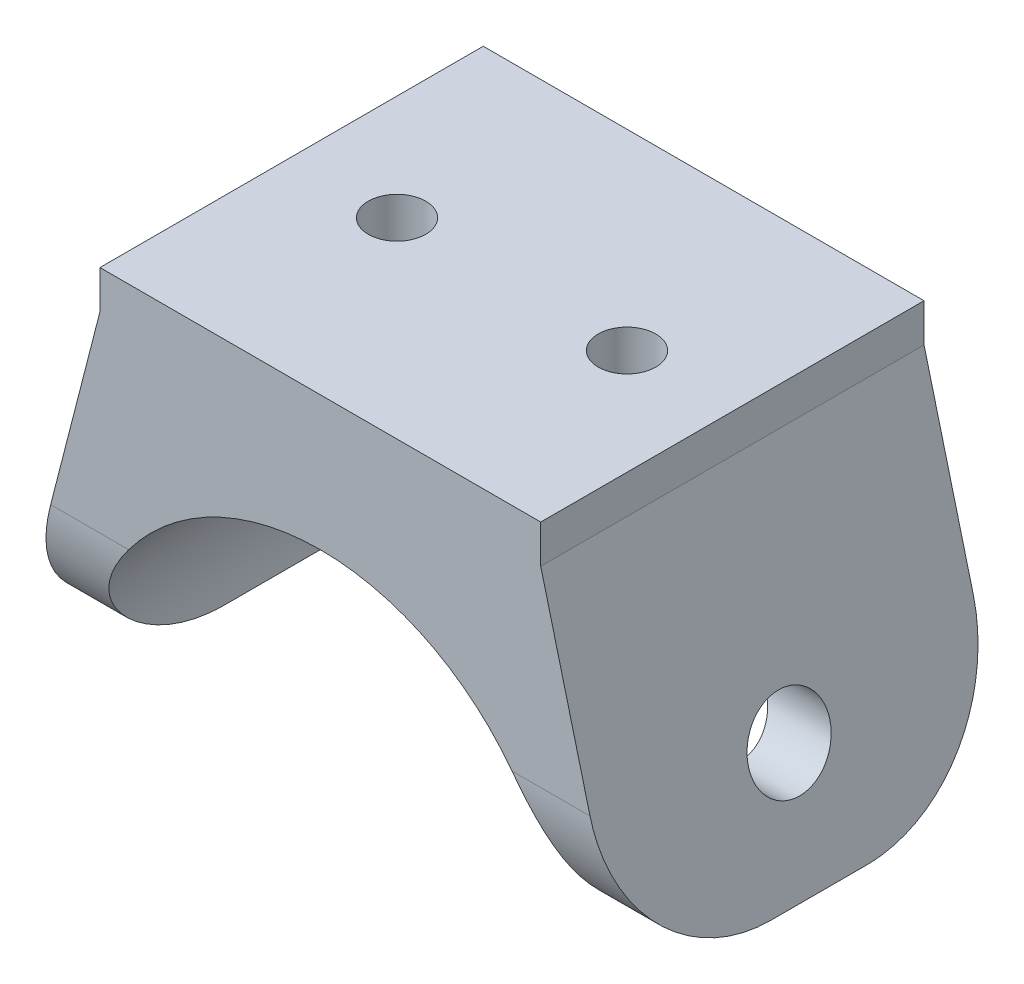
SolidWorks part; units mm, degrees
ref_plane "前基準面" through (0, 0, 0) normal (0, 0, 1) x (1, 0, 0)
ref_plane "上基準面" through (0, 0, 0) normal (0, 1, 0) x (1, 0, 0)
ref_plane "右基準面" through (0, 0, 0) normal (1, 0, 0) x (0, 0, -1)
sketch "草圖1" plane through (0, 0, 0) normal (0, 0, 1) x (1, 0, 0)
  line L0 (-23, 35) -> (-32, 0)
  line L1 (-23, 39) -> (23, 39)
  line L2 (-23, 39) -> (-23, 35)
  line L4 (23, 39) -> (23, 35)
  line L5 (-32, 0) -> (-25, 0)
  line L6 (32, 0) -> (23, 35)
  line L7 (25, 0) -> (32, 0)
  arc A0 (25, 0) -> (-25, 0) centre (0, 0) ccw
  dimension "D4" = 50
  dimension "D1" = 46
  dimension "D2" = 4
  dimension "D3" = 64
  dimension "D5" = 39
extrude "填料-伸長1" add sketch "草圖1" along normal blind 40
sketch "草圖2" plane through (0, 39, 0) normal (0, 1, 0) x (1, 0, 0)
  line L0 (0, 5.4826) -> (0, -42.1633) construction
  line L1 (-36.6182, -20) -> (35.4385, -20) construction
  circle A0 centre (-12, -20) radius 3
  circle A1 centre (12, -20) radius 3
  dimension "D1" = 6
  dimension "D2" = 6
  dimension "D3" = 12
  dimension "D4" = 12
extrude "除料-伸長1" cut sketch "草圖2" against normal blind 14
sketch "草圖3" plane through (0, 0, 0) normal (1, 0, 0) x (0, 0, -1)
  line L0 (-20, 44.9808) -> (-20, -1.3539) construction
  line L1 (-40, 39) -> (0, 39) construction
  circle A0 centre (-20, 12) radius 4.25
  dimension "D1" = 8.5
  dimension "D2" = 27
extrude "除料-伸長2" cut sketch "草圖3" against normal through all both and the other way through all
fillet "圓角1" radius 15 4 edges at (-28.5, 0, 0) (28.5, 0, 0) (28.5, 0, 40) (-28.5, 0, 40)
